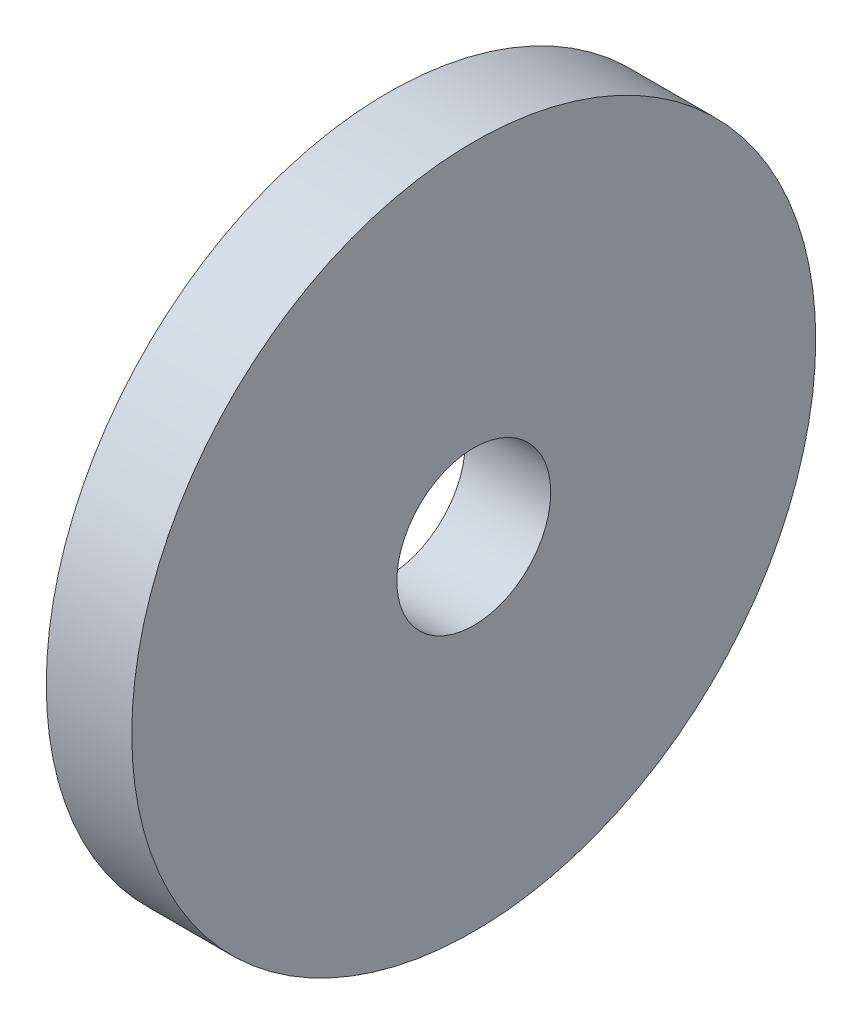
SolidWorks part; units mm, degrees
ref_plane "Front Plane" through (0, 0, 0) normal (0, 0, 1) x (1, 0, 0)
ref_plane "Top Plane" through (0, 0, 0) normal (0, 1, 0) x (1, 0, 0)
ref_plane "Right Plane" through (0, 0, 0) normal (1, 0, 0) x (0, 0, -1)
sketch "Sketch1" plane through (0, 0, 0) normal (1, 0, 0) x (0, 0, -1)
  circle A0 centre (0, 0) radius 20
  circle A1 centre (0, 0) radius 4.5
  dimension "D1" = 9
  dimension "D2" = 40
extrude "Boss-Extrude1" add sketch "Sketch1" along normal blind 5
